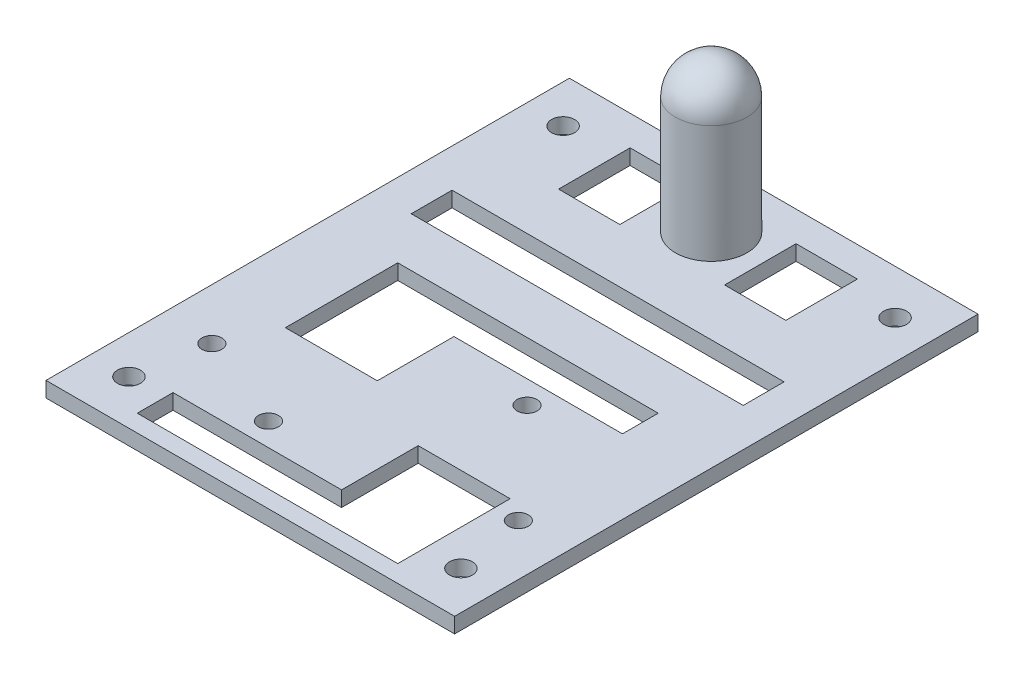
SolidWorks part; units mm, degrees
material "PF"
ref_plane "Plan de face" through (0, 0, 0) normal (0, 0, 1) x (1, 0, 0)
ref_plane "Plan de dessus" through (0, 0, 0) normal (0, 1, 0) x (1, 0, 0)
ref_plane "Plan de droite" through (0, 0, 0) normal (1, 0, 0) x (0, 0, -1)
sketch "Esquisse1" plane through (0, 0, 0) normal (0, 1, 0) x (1, 0, 0)
  circle A0 centre (0, 0) radius 65
  dimension "D1" = 130
extrude "disque" add sketch "Esquisse1" along normal blind 3
sketch "Esquisse3" plane through (0, 3, 0) normal (0, 1, 0) x (1, 0, 0)
  line L0 (0, 0) -> (0, 63.5107) construction
  line L1 (-40, 100) -> (-40, -100)
  line L2 (-40, -100) -> (-70.4664, -100)
  line L3 (-70.4664, -100) -> (-70.4664, 100)
  line L4 (-70.4664, 100) -> (-40, 100)
  line L5 (40, -100) -> (70.4664, -100)
  line L6 (70.4664, -100) -> (70.4664, 100)
  line L7 (70.4664, 100) -> (40, 100)
  line L8 (40, 100) -> (40, -100)
  line L9 (-40, 0) -> (0, 0) construction
  dimension "D1" = 40
  dimension "D2" = 200
extrude "cotés" cut sketch "Esquisse3" against normal through all
sketch "Esquisse4" plane through (0, 3, 0) normal (0, 1, 0) x (1, 0, 0)
  line L0 (-40, -28.7652) -> (40, -28.7652) construction
  line L1 (0, 65) -> (0, -65) construction
  line L2 (-40, 51.2348) -> (53.9104, 51.2348) construction
  line L3 (-40, 26.2348) -> (58.169, 26.2348) construction
  line L4 (-40, -51.2348) -> (-40, 51.2348) construction
  arc A0 (40, 51.2348) -> (-40, 51.2348) centre (0, 0) ccw construction
  arc A1 (-40, -51.2348) -> (40, -51.2348) centre (0, 0) ccw construction
  point P2 (0, -28.7652)
  point P11 (0, 58.6194)
  dimension "D1" = 80
  dimension "D2" = 55
sketch "Esquisse10" plane through (0, 3, 0) normal (0, 1, 0) x (1, 0, 0)
  line L1 (32.5, -42.5) -> (-32.5, -42.5)
  line L2 (32.5, -42.5) -> (32.5, 42.5)
  line L3 (32.5, 42.5) -> (-32.5, 42.5)
  line L4 (-32.5, -42.5) -> (-32.5, 42.5)
  line L5 (32.5, -42.5) -> (-32.5, 42.5) construction
  line L6 (32.5, 42.5) -> (-32.5, -42.5) construction
  point P0 (0, 0)
  dimension "D1" = 85
  dimension "D2" = 65
hole_wizard "Dégagement M3.52" positions "Esquisse8" profile "Esquisse7" hole size "M3.5" standard "Iso" end condition through all
sketch "Esquisse8" plane through (0, 3, 0) normal (0, 1, 0) x (1, 0, 0)
  line L0 (-40, -28.7652) -> (40, -28.7652) construction
  line L1 (0, 65) -> (0, -65) construction
  point P0 (-30, -28.7652)
  dimension "D1" = 30
sketch "Esquisse7" plane through (-30, 3, 28.7652) normal (1, 0, 0) x (0, 0, 1)
  line L0 (0, 0) -> (0, 3)
  line L1 (0, 3) -> (1.95, 3)
  line L2 (1.95, 3) -> (1.95, 0)
  line L5 (1.95, 0) -> (0, 0)
  line L11 (0, -6.35) -> (0, 107.95) construction
  dimension "Diamètre du perçage jusqu'au prochain" = 3.9
  dimension "Profondeur du perçage jusqu'au prochain" = 3
ref_plane "Plan1" through (0, 0, 0) normal (-1, 0, 0) x (0, 0, 1)
mirror "Symétrie1" about plane through (0, 0, 0) normal (-1, 0, 0) of "Dégagement M3.52"
hole_wizard "Dégagement M42" positions "Esquisse12" profile "Esquisse13" hole size "M4" standard "Iso" end condition through all
sketch "Esquisse12" plane through (0, 3, 0) normal (0, 1, 0) x (1, 0, 0)
  point P0 (-32.5, 42.5)
  point P3 (32.5, 42.5)
  point P6 (32.5, -42.5)
  point P9 (-32.5, -42.5)
sketch "Esquisse13" plane through (-32.5, 3, -42.5) normal (1, 0, 0) x (0, 0, 1)
  line L0 (0, 0) -> (0, 3)
  line L1 (0, 3) -> (2.25, 3)
  line L2 (2.25, 3) -> (2.25, 0)
  line L5 (2.25, 0) -> (0, 0)
  line L11 (0, -6.35) -> (0, 107.95) construction
  dimension "Diamètre du perçage jusqu'au prochain" = 4.5
  dimension "Profondeur du perçage jusqu'au prochain" = 3
ref_plane "Plan2" through (0, 0, 0) normal (-1, 0, 0) x (0, 0, 1)
sketch "Esquisse14" plane through (0, 0, 0) normal (-1, 0, 0) x (0, 0, 1)
  line L0 (-39, 3) -> (-39, 49.2918) construction
  line L1 (-65, 3) -> (65, 3) construction
  line L2 (-35, 3) -> (-32, 3)
  line L3 (-32, 3) -> (-32, 26)
  line L4 (-39, 33) -> (-52.5869, 33) construction
  line L5 (-35, 26) -> (-35, 3)
  line L6 (-39, 3) -> (-35, 3) construction
  line L7 (-39, 33) -> (-39, 30)
  arc A0 (-32, 26) -> (-39, 33) centre (-39, 26) ccw
  arc A1 (-35, 26) -> (-39, 30) centre (-39, 26) ccw
  dimension "D1" = 3
  dimension "D2" = 30
  dimension "D3" = 4
revolve "Révolution1" add sketch "Esquisse14" angle 360 about L0
sketch "Esquisse15" plane through (0, 0, 0) normal (0, -1, 0) x (1, 0, 0)
  line L1 (40, 51.2348) -> (-49.8632, 51.2348)
  line L2 (40, 51.2348) -> (40, 83.331)
  line L3 (40, 83.331) -> (-49.8632, 83.331)
  line L4 (-49.8632, 51.2348) -> (-49.8632, 83.331)
extrude "Enlèv. mat.-Extru.1" cut sketch "Esquisse15" against normal through all
ref_plane "Plan3" through (0, 0, 0) normal (0, -1, 0) x (-1, 0, 0)
sketch "emplacement compos" plane through (0, 0, 0) normal (0, -1, 0) x (-1, 0, 0)
  line L0 (0, 72.5668) -> (0, -66.1044) construction
  line L1 (-40, -5.1284) -> (64.5168, -5.1284) construction
  line L2 (-40, 51.2348) -> (-40, -51.2348) construction
  line L3 (-40, 51.2348) -> (63.3599, 51.2348) construction
  line L4 (32.5, 6.5) -> (-32.5, 6.5)
  line L5 (32.5, 6.5) -> (32.5, 25.5)
  line L6 (32.5, 25.5) -> (-32.5, 25.5)
  line L7 (-32.5, 6.5) -> (-32.5, 25.5)
  line L8 (32.5, 6.5) -> (-32.5, 25.5) construction
  line L9 (32.5, 25.5) -> (-32.5, 6.5) construction
  line L10 (24, 28.8674) -> (-24, 28.8674)
  line L11 (24, 28.8674) -> (24, 47.8674)
  line L12 (24, 47.8674) -> (-24, 47.8674)
  line L13 (-24, 28.8674) -> (-24, 47.8674)
  line L14 (24, 28.8674) -> (-24, 47.8674) construction
  line L15 (24, 47.8674) -> (-24, 28.8674) construction
  line L16 (-40, 16) -> (-32.5, 16) construction
  line L17 (32.5, 38.3674) -> (40, 38.3674) construction
  line L18 (40, -51.2348) -> (40, 51.2348) construction
  line L19 (-24, 38.3674) -> (-40, 38.3674) construction
  line L20 (25.5, -47.8674) -> (-25.5, -47.8674)
  line L21 (25.5, -47.8674) -> (25.5, 3.1326)
  line L22 (25.5, 3.1326) -> (-25.5, 3.1326)
  line L23 (-25.5, -47.8674) -> (-25.5, 3.1326)
  line L24 (25.5, -47.8674) -> (-25.5, 3.1326) construction
  line L25 (25.5, 3.1326) -> (-25.5, -47.8674) construction
  line L26 (24, 38.3674) -> (40, 38.3674) construction
  line L27 (-25.5, -22.3674) -> (-40, -22.3674) construction
  line L28 (25.5, -22.3674) -> (40, -22.3674) construction
  line L29 (40, -51.2348) -> (-40, -51.2348) construction
  line L30 (-11.3137, 51.2348) -> (-11.3137, 47.8674) construction
  line L31 (11.3137, -36.3674) -> (-11.3137, -36.3674)
  line L32 (11.3137, -36.3674) -> (11.3137, -8.3674)
  line L33 (11.3137, -8.3674) -> (-11.3137, -8.3674)
  line L34 (-11.3137, -36.3674) -> (-11.3137, -8.3674)
  line L35 (11.3137, -36.3674) -> (-11.3137, -8.3674) construction
  line L36 (11.3137, -8.3674) -> (-11.3137, -36.3674) construction
  line L37 (-11.3137, 28.8674) -> (-11.3137, 25.5) construction
  line L39 (-11.3137, -47.8674) -> (-11.3137, -51.2348) construction
  point P7 (0, 16)
  point P12 (0, 38.3674)
  point P26 (0, -22.3674)
  point P40 (0, -22.3674)
  dimension "D3" = 19
  dimension "D4" = 65
  dimension "D5" = 48
  dimension "D6" = 51
  dimension "D8" = 36
  dimension "D9" = 28
hole_wizard "Dégagement M3.53" positions "Esquisse20" profile "Esquisse19" hole size "M3.5" standard "Iso"
sketch "Esquisse20" plane through (0, 0, 0) normal (0, -1, 0) x (-1, 0, 0)
  point P0 (-11.3137, -8.3674)
  point P3 (11.3137, -36.3674)
sketch "Esquisse19" plane through (11.3137, 0, 8.3674) normal (1, 0, 0) x (0, 0, -1)
  line L0 (0, 0) -> (0, 4.1717)
  line L1 (0, 4.1717) -> (1.95, 3)
  line L2 (1.95, 3) -> (1.95, 0)
  line L5 (1.95, 0) -> (0, 0)
  line L10 (0, 4.1717) -> (-1.95, 3) construction
  line L11 (0, -6.35) -> (0, 107.95) construction
  dimension "Diamètre du perçage" = 3.9
  dimension "Profondeur du perçage" = 3
  dimension "Angle de pointe" = 118
sketch "Esquisse22" plane through (0, 0, 0) normal (0, -1, 0) x (-1, 0, 0)
  line L0 (32.5, 6.5) -> (32.5, 25.5) construction
  line L5 (-32.5, 16) -> (32.5, 16) construction
  line L6 (-32.5, 6.5) -> (-32.5, 25.5) construction
  line L7 (-24, 38.3674) -> (24, 38.3674) construction
  line L8 (-24, 28.8674) -> (-24, 47.8674) construction
  line L9 (24, 28.8674) -> (24, 47.8674) construction
  line L10 (-24, 28.8674) -> (24, 28.8674)
  line L11 (-24, 28.8674) -> (-24, 34.8674)
  line L12 (-24, 34.8674) -> (24, 34.8674)
  line L13 (24, 28.8674) -> (24, 34.8674)
  line L14 (24, 47.8674) -> (24, 41.8674)
  line L15 (-24, 47.8674) -> (24, 47.8674)
  line L16 (-24, 47.8674) -> (-24, 41.8674)
  line L17 (-24, 41.8674) -> (24, 41.8674)
  line L18 (32.5, 20.7663) -> (32.5, 12.7663)
  line L19 (-32.5, 20.7663) -> (32.5, 20.7663)
  line L20 (-32.5, 20.7663) -> (-32.5, 12.7663)
  line L21 (-32.5, 12.7663) -> (32.5, 12.7663)
  line L22 (25.5, -47.8674) -> (25.5, 3.1326) construction
  line L23 (-25.5, -47.8674) -> (25.5, -47.8674)
  line L24 (-25.5, -47.8674) -> (-25.5, -40.8674)
  line L25 (-25.5, -40.8674) -> (25.5, -40.8674)
  line L26 (25.5, -47.8674) -> (25.5, -40.8674)
  line L28 (25.5, 3.1326) -> (-25.5, 3.1326)
  line L29 (25.5, 3.1326) -> (25.5, -3.8674)
  line L30 (25.5, -3.8674) -> (-25.5, -3.8674)
  line L31 (-25.5, 3.1326) -> (-25.5, -3.8674)
  line L32 (-40, 51.2348) -> (73.2485, 51.2348)
  line L33 (-40, 51.2348) -> (-40, 85.8477)
  line L34 (-40, 85.8477) -> (73.2485, 85.8477)
  line L35 (73.2485, 51.2348) -> (73.2485, 85.8477)
  dimension "D1" = 8
  dimension "D2" = 7
extrude "Enlèv. mat.-Extru.3" cut sketch "Esquisse22" against normal blind 10 contours L32 L35 L34 L33 | L28 L31 L30 L29 | L23 L26 L25 L24 | L19 L18 L21 L20
sketch "Esquisse23" plane through (0, 3, 0) normal (0, 1, 0) x (1, 0, 0)
  line L0 (0, 79.4802) -> (0, -109.9497) construction
  line L1 (-22.25, 31.3674) -> (-10.25, 31.3674)
  line L2 (-22.25, 31.3674) -> (-22.25, 45.3674)
  line L3 (-22.25, 45.3674) -> (-10.25, 45.3674)
  line L4 (-10.25, 31.3674) -> (-10.25, 45.3674)
  line L5 (10.25, 31.3674) -> (10.25, 45.3674)
  line L6 (22.25, 31.3674) -> (10.25, 31.3674)
  line L7 (22.25, 31.3674) -> (22.25, 45.3674)
  line L8 (22.25, 45.3674) -> (10.25, 45.3674)
  line L9 (-16.25, 45.3674) -> (-16.25, 51.2348) construction
  line L10 (-40, 51.2348) -> (40, 51.2348) construction
  line L11 (-16.25, 31.3674) -> (-16.25, 25.5) construction
  line L12 (-32.5, 25.5) -> (32.5, 25.5) construction
  line L13 (-32.5, 42.5) -> (-32.5, 59.1682) construction
  line L14 (-32.5, 42.5) -> (-22.25, 42.5) construction
  line L15 (-10.25, 38.3674) -> (0, 38.3674) construction
  point P4 (-23, 40.5)
  dimension "D1" = 12
  dimension "D2" = 14
extrude "Enlèv. mat.-Extru.4" cut sketch "Esquisse23" against normal blind 10
sketch "Esquisse24" plane through (0, 3, 0) normal (0, 1, 0) x (1, 0, 0)
  line L1 (-25.5, -3.8674) -> (-7.5, -3.8674)
  line L2 (-25.5, -3.8674) -> (-25.5, -18.8674)
  line L3 (-25.5, -18.8674) -> (-7.5, -18.8674)
  line L4 (-7.5, -3.8674) -> (-7.5, -18.8674)
  line L5 (25.5, -40.8674) -> (7.5, -40.8674)
  line L6 (25.5, -40.8674) -> (25.5, -25.8674)
  line L7 (25.5, -25.8674) -> (7.5, -25.8674)
  line L8 (7.5, -40.8674) -> (7.5, -25.8674)
  dimension "D1" = 15
  dimension "D2" = 15
extrude "Enlèv. mat.-Extru.5" cut sketch "Esquisse24" against normal blind 10
sketch "emplacement moteur" plane through (0, 3, 0) normal (0, 1, 0) x (1, 0, 0)
  line L1 (-29, -36.2348) -> (29, -36.2348)
  line L2 (-29, -36.2348) -> (-29, 23.7652)
  line L3 (-29, 23.7652) -> (29, 23.7652)
  line L4 (29, -36.2348) -> (29, 23.7652)
  line L6 (40, -51.2348) -> (-40, -51.2348) construction
  line L7 (-29, -9.6275) -> (-40, -9.6275) construction
  line L8 (-40, -51.2348) -> (-40, 51.2348) construction
  line L9 (29, -9.6275) -> (40, -9.6275) construction
  line L10 (40, 51.2348) -> (40, -51.2348) construction
  dimension "D1" = 15
  dimension "D2" = 60
  dimension "D3" = 58
